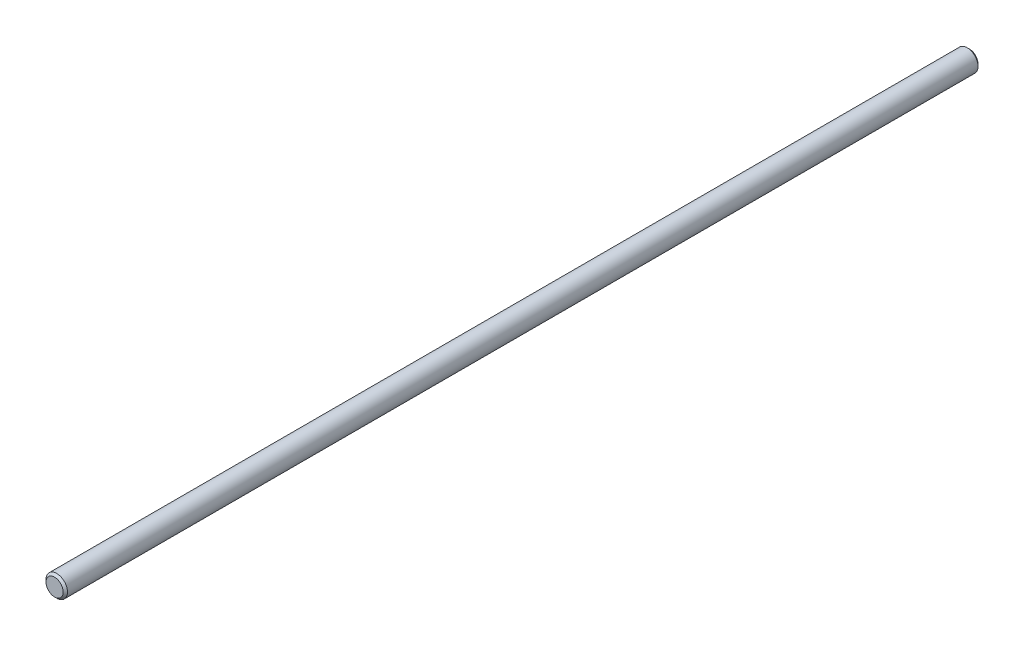
SolidWorks part; units mm, degrees
ref_plane "Front" through (0, 0, 0) normal (0, 0, 1) x (1, 0, 0)
ref_plane "Top" through (0, 0, 0) normal (0, 1, 0) x (1, 0, 0)
ref_plane "Right" through (0, 0, 0) normal (1, 0, 0) x (0, 0, -1)
sketch "Sketch1" plane through (0, 0, 0) normal (0, 0, 1) x (1, 0, 0)
  circle A0 centre (0, 0) radius 5
  dimension "D1" = 10
extrude "Extrude1" add sketch "Sketch1" along normal mid plane 426.212
chamfer "Chamfer1" distance 1 angle 45 2 edges at (5, 0, -213.106) (5, 0, 213.106)
equation "\"D1@Chamfer1\" = \"D1@Sketch1\" * .1"
